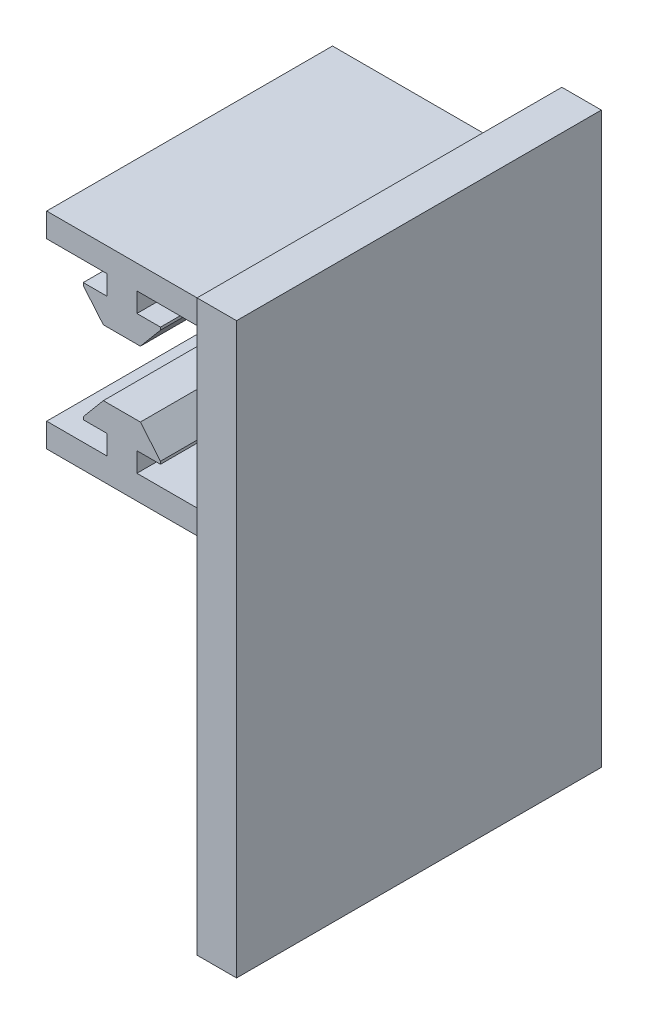
SolidWorks part; units mm, degrees
ref_plane "Front Plane" through (0, 0, 0) normal (0, 0, 1) x (1, 0, 0)
ref_plane "Top Plane" through (0, 0, 0) normal (0, 1, 0) x (1, 0, 0)
ref_plane "Right Plane" through (0, 0, 0) normal (1, 0, 0) x (0, 0, -1)
sketch "Sketch1" plane through (0, 0, 0) normal (0, 0, 1) x (1, 0, 0)
  line L0 (-19.05, 8.89) -> (19.05, 8.89)
  line L1 (-19.05, 8.89) -> (-19.05, 2.794)
  line L2 (-19.05, 2.794) -> (-3.81, 2.794)
  line L3 (-3.81, 2.794) -> (-3.81, -2.159)
  line L4 (-3.81, -2.159) -> (-9.779, -2.159)
  line L5 (-9.779, -2.159) -> (-9.779, -2.8321)
  line L6 (-9.779, -2.8321) -> (-4.6958, -8.89)
  line L7 (-4.6958, -8.89) -> (4.6958, -8.89)
  line L8 (0, -8.89) -> (0, 8.89) construction
  line L9 (4.6958, -8.89) -> (9.779, -2.8321)
  line L10 (9.779, -2.8321) -> (9.779, -2.159)
  line L11 (3.81, -2.159) -> (9.779, -2.159)
  line L12 (3.81, 2.794) -> (3.81, -2.159)
  line L13 (19.05, 2.794) -> (3.81, 2.794)
  line L14 (19.05, 8.89) -> (19.05, 2.794)
  dimension "D2" = 38.1
  dimension "D1" = 17.78
  dimension "D3" = 7.62
  dimension "D4" = 19.558
  dimension "D5" = 50
  dimension "D6" = 4.953
  dimension "D7" = 6.731
  dimension "D8" = 6.0579
extrude "Boss-Extrude1" add sketch "Sketch1" along normal mid plane 914.4
ref_plane "Contact Plane 1" through (0, 2.794, 0) normal (0, -1, 0) x (-1, 0, 0)
sketch "Sketch2" plane through (0, 0, -457.2) normal (0, 0, -1) x (-1, 0, 0)
  line L1 (-21.0255, 11.7996) -> (21.0255, 11.7996)
  line L2 (-21.0255, 11.7996) -> (-21.0255, -11.7996)
  line L3 (-21.0255, -11.7996) -> (21.0255, -11.7996)
  line L4 (21.0255, 11.7996) -> (21.0255, -11.7996)
  line L5 (-21.0255, 11.7996) -> (21.0255, -11.7996) construction
  line L6 (-21.0255, -11.7996) -> (21.0255, 11.7996) construction
  point P0 (0, 0)
extrude "Cut-Extrude1" cut sketch "Sketch2" against normal blind 800
ref_plane "Plane3" through (0, -17.206, 0) normal (0, -1, 0) x (-1, 0, 0)
sketch "Sketch3" plane through (19.05, 0, 0) normal (1, 0, 0) x (0, 0, -1)
  line L1 (-457.2, 8.89) -> (-342.8, 8.89)
  line L2 (-457.2, 8.89) -> (-457.2, -47.5467)
  line L3 (-457.2, -47.5467) -> (-342.8, -47.5467)
  line L4 (-342.8, 8.89) -> (-342.8, -47.5467)
extrude "Boss-Extrude2" add sketch "Sketch3" along normal blind 10
mirror "Mirror1" about plane through (0, -17.206, 0) normal (0, -1, 0) of "Boss-Extrude1", "Cut-Extrude1"
sketch "Sketch4" plane through (19.05, 0, 0) normal (-1, 0, 0) x (0, 0, 1)
  line L1 (342.8, -47.5467) -> (457.2, -47.5467)
  line L2 (342.8, -47.5467) -> (342.8, -43.302)
  line L3 (342.8, -43.302) -> (457.2, -43.302)
  line L4 (457.2, -47.5467) -> (457.2, -43.302)
extrude "Cut-Extrude2" cut sketch "Sketch4" against normal blind 10
sketch "Sketch7" plane through (0, 0, 457.2) normal (0, 0, 1) x (1, 0, 0)
  line L1 (-19.05, 8.89) -> (29.05, 8.89)
  line L2 (-19.05, 8.89) -> (-19.05, -43.302)
  line L3 (-19.05, -43.302) -> (29.05, -43.302)
  line L4 (29.05, 8.89) -> (29.05, -43.302)
extrude "Cut-Extrude3" cut sketch "Sketch7" against normal blind 42
sketch "Sketch8" plane through (0, 0, 342.8) normal (0, 0, -1) x (-1, 0, 0)
  line L1 (-19.05, 2.794) -> (-19.95, 2.794)
  line L2 (-19.05, 2.794) -> (-19.05, -37.206)
  line L3 (-19.05, -37.206) -> (-19.95, -37.206)
  line L4 (-19.95, 2.794) -> (-19.95, -37.206)
  dimension "D1" = 0.9
extrude "Cut-Extrude4" cut sketch "Sketch8" against normal blind 90
sketch "Sketch10" plane through (29.05, 0, 0) normal (1, 0, 0) x (0, 0, -1)
  line L0 (-8.877, -17.206) -> (8.877, -17.206) construction
  line L1 (-425.2, 18.89) -> (-332.8, 18.89)
  line L2 (-425.2, 18.89) -> (-425.2, -53.302)
  line L3 (-425.2, -53.302) -> (-332.8, -53.302) construction
  line L4 (-332.8, 18.89) -> (-332.8, -53.302)
  line L5 (-425.2, 18.89) -> (-332.8, -53.302) construction
  line L6 (-425.2, -53.302) -> (-332.8, 18.89) construction
  line L7 (-342.8, -43.302) -> (-342.8, 8.89) construction
  line L8 (-415.2, -43.302) -> (-415.2, 8.89) construction
  line L9 (-415.2, -43.302) -> (-342.8, -43.302) construction
  line L12 (-425.2, -53.302) -> (-332.8, -53.302) construction
  line L13 (-425.2, -53.302) -> (-425.2, -125.302)
  line L14 (-425.2, -125.302) -> (-332.8, -125.302)
  line L15 (-332.8, -53.302) -> (-332.8, -125.302)
  point P0 (-379, -17.206)
  dimension "D1" = 10
  dimension "D2" = 10
  dimension "D3" = 10
  dimension "D4" = 72
extrude "Boss-Extrude3" add sketch "Sketch10" along normal blind 10
equation "\"D8@Sketch1\"=\"D7@Sketch1\"*.90"
